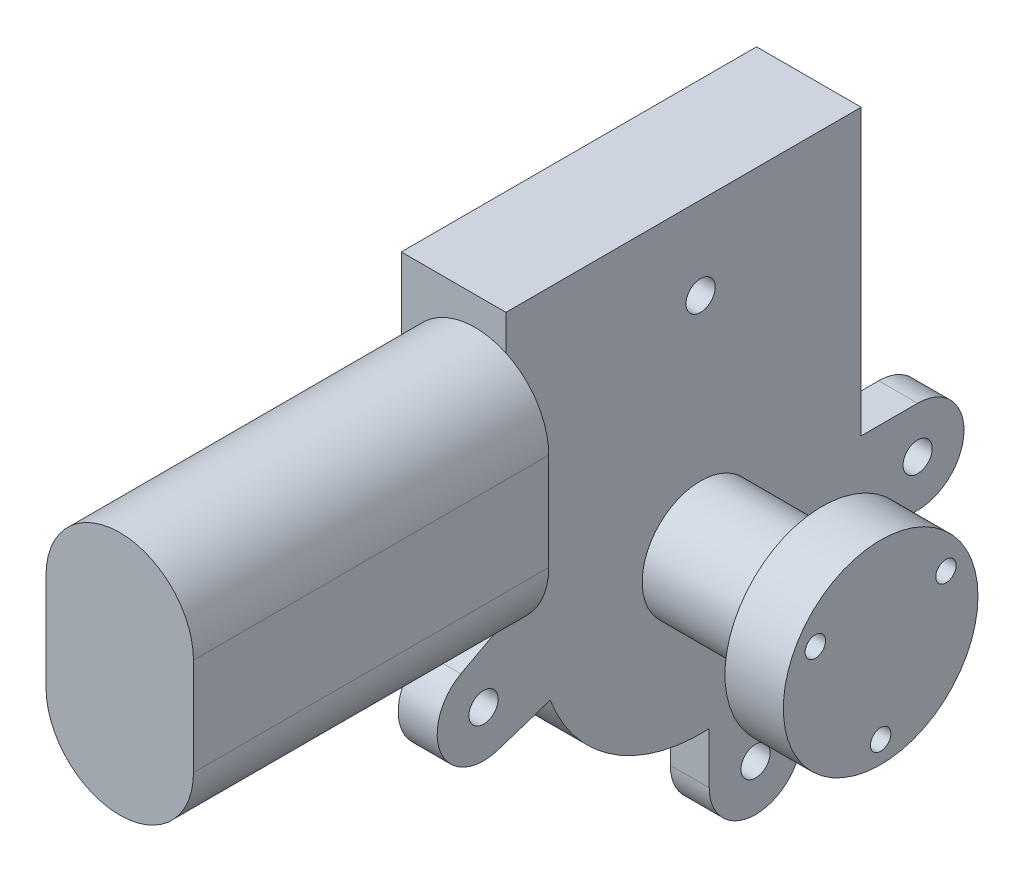
SolidWorks part; units mm, degrees
material "5052-H32"
ref_plane "Front Plane" through (0, 0, 0) normal (0, 0, 1) x (1, 0, 0)
ref_plane "Top Plane" through (0, 0, 0) normal (0, 1, 0) x (1, 0, 0)
ref_plane "Right Plane" through (0, 0, 0) normal (1, 0, 0) x (0, 0, -1)
other "Center of Mass"
sketch "Sketch1" plane through (0, 0, 0) normal (1, 0, 0) x (0, 0, -1)
  circle A0 centre (-33, 0) radius 33
  dimension "D1" = 66
extrude "Boss-Extrude1" add sketch "Sketch1" along normal blind 21.5
sketch "Sketch4" plane through (21.5, 0, 0) normal (1, 0, 0) x (0, 0, -1)
  circle A0 centre (-33, 0) radius 20
  dimension "D1" = 40
extrude "Boss-Extrude4" add sketch "Sketch4" along normal blind 37
sketch "Sketch6" plane through (0, 0, 0) normal (0, 0, 1) x (1, 0, 0)
  line L0 (21.5, -33) -> (21.5, 33) construction
  line L1 (0, 0) -> (21.5, 0)
  line L2 (0, 0) -> (0, 62)
  line L3 (0, 62) -> (21.5, 62)
  line L4 (21.5, 0) -> (21.5, 62)
  dimension "D1" = 62
extrude "Boss-Extrude5" add sketch "Sketch6" along normal blind 73
sketch "Sketch7" plane through (0, 0, 73) normal (0, 0, 1) x (1, 0, 0)
  line L0 (15.15, 41) -> (15.15, 21) construction
  line L1 (30.3, 41) -> (30.3, 21)
  line L2 (0, 41) -> (0, 21)
  line L3 (0, 62) -> (0, 0) construction
  arc A0 (30.3, 41) -> (0, 41) centre (15.15, 41) ccw
  arc A1 (0, 21) -> (30.3, 21) centre (15.15, 21) ccw
  point P2 (15.15, 31)
  point P19 (0, 31)
  dimension "D1" = 20
  dimension "D2" = 30.3
extrude "Boss-Extrude6" add sketch "Sketch7" along normal blind 73
sketch "Sketch9" plane through (21.5, 0, 0) normal (1, 0, 0) x (0, 0, -1)
  line L0 (-33, -33) -> (-33, 45) construction
  line L1 (11.6, 3.525) -> (0, 3.525)
  line L2 (0, 0) -> (0, 62) construction
  line L3 (11.6, -15.525) -> (-3.88, -15.525)
  line L4 (-12.175, -43.5) -> (-12.175, -25.5992)
  line L5 (-31.225, -32.9522) -> (-31.225, -43.5)
  line L6 (-82.2696, 2.3019) -> (-73, 7.245)
  line L7 (-74.6479, -15.056) -> (-63.9106, -11.5557)
  line L8 (-73, 7.245) -> (-63.9106, 7.245)
  line L9 (-63.9106, 7.245) -> (-63.9106, -11.5557)
  line L10 (-31.225, -32.9522) -> (-12.175, -25.5992)
  line L11 (0, 3.525) -> (-3.88, -15.525)
  arc A0 (-66, 0) -> (0, 0) centre (-33, 0) ccw construction
  arc A1 (11.6, 3.525) -> (11.6, -15.525) centre (11.6, -6) cw
  arc A2 (-12.175, -43.5) -> (-31.225, -43.5) centre (-21.7, -43.5) cw
  arc A3 (-82.2696, 2.3019) -> (-74.6479, -15.056) centre (-77.6, -6) ccw
  point P0 (11.6, -6)
  point P1 (-21.7, -43.5)
  point P2 (-77.6, -6)
  point P3 (-33, 45)
  dimension "D1" = 44.6
  dimension "D5" = 44.6
  dimension "D7" = 45
  dimension "D8" = 9.525
  dimension "D9" = 9.525
  dimension "D10" = 9.525
  dimension "D2" = 6
  dimension "D3" = 11.3
  dimension "D4" = 43.5
  dimension "D6" = 6
extrude "Boss-Extrude7" add sketch "Sketch9" against normal blind 8
hole_wizard "M6x1.0 Tapped Hole1" positions "Sketch10" profile "Sketch11" tap size "M6x1.0" standard "ANSI Metric"
sketch "Sketch10" plane through (21.5, 0, 0) normal (1, 0, 0) x (0, 0, -1)
  point P0 (-33, 45)
  point P3 (11.6, -6)
  point P6 (-21.7, -43.5)
  point P9 (-77.6, -6)
sketch "Sketch11" plane through (21.5, 45, 33) normal (0, 1, 0) x (0, 0, -1)
  line L0 (0, 0) -> (0, 16.4922)
  line L1 (0, 16.4922) -> (2.5, 14.99)
  line L2 (2.5, 14.99) -> (2.5, 11.94)
  line L3 (2.5, 11.94) -> (3, 11.94)
  line L4 (3, 11.94) -> (3, 0)
  line L5 (3, 0) -> (0, 0)
  line L10 (0, 16.4922) -> (-2.5, 14.99) construction
  line L11 (0, -6.35) -> (0, 107.95) construction
  dimension "Tap Drill Dia." = 5
  dimension "Tap Drill Depth" = 14.99
  dimension "Thread Major Dia." = 6
  dimension "Thread Depth" = 11.94
  dimension "Drill Angle" = 118
hole_wizard "M5x0.8 Tapped Hole1" positions "Sketch12" profile "Sketch13" tap size "M5x0.8" standard "ANSI Metric"
sketch "Sketch12" plane through (58.5, 0, 0) normal (1, 0, 0) x (0, 0, -1)
  line L0 (-33, -33) -> (-33, 45) construction
  line L1 (-33, -15.5) -> (-33, 0) construction
  line L4 (-33, -0.3676) -> (-33, 0) construction
  line L5 (-33, 0) -> (-46.4234, 7.75) construction
  line L7 (-33, 0) -> (-19.5766, 7.75) construction
  circle A0 centre (-33, 0) radius 15.5 construction
  point P9 (-33, -15.5)
  point P10 (-46.4234, 7.75)
  point P12 (-19.5766, 7.75)
  dimension "D1" = 31
  dimension "D2" = 120
  dimension "D3" = 120
sketch "Sketch13" plane through (58.5, 7.75, 19.5766) normal (0, 1, 0) x (0, 0, -1)
  line L0 (0, 0) -> (0, 13.4538)
  line L1 (0, 13.4538) -> (2.1, 12.192)
  line L2 (2.1, 12.192) -> (2.1, 0)
  line L5 (2.1, 0) -> (0, 0)
  line L10 (0, 13.4538) -> (-2.1, 12.192) construction
  line L11 (0, -6.35) -> (0, 107.95) construction
  dimension "Tap Drill Dia." = 4.2
  dimension "Tap Drill Depth" = 12.192
  dimension "Drill Angle" = 118
cosmetic thread "Hole Thread5" parameters "D1"=9.906, "D2"=5
cosmetic thread "Hole Thread6" parameters "D1"=9.906, "D2"=5
cosmetic thread "Hole Thread7" parameters "D1"=9.906, "D2"=5
sketch "Sketch14" plane through (0, 0, 0) normal (0, 1, 0) x (1, 0, 0)
  line L0 (46.5, -53) -> (46.5, -45)
  line L1 (21.5, -53) -> (58.5, -53) construction
  line L2 (46.5, -45) -> (21.5, -45)
  line L3 (21.5, -45) -> (21.5, -53)
  line L4 (21.5, -53) -> (58.5, -53) construction
  line L5 (21.5, -53) -> (46.5, -53)
  line L6 (58.5, -53) -> (58.5, -13) construction
  line L7 (21.5, -53) -> (21.5, -13) construction
  line L8 (58.5, -33) -> (21.5, -33) construction
  dimension "D1" = 8
  dimension "D2" = 12
revolve "Cut-Revolve1" cut sketch "Sketch14" angle 360 about L8
